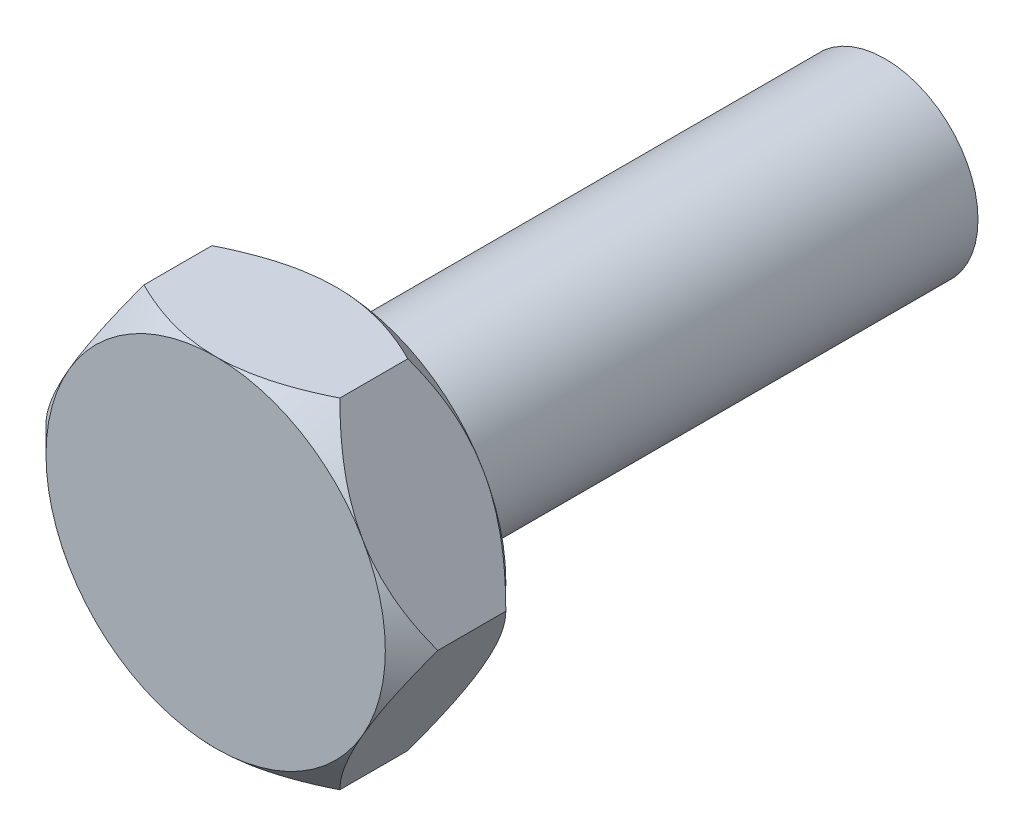
SolidWorks part; units mm, degrees
ref_plane "Front Plane" through (0, 0, 0) normal (0, 0, 1) x (1, 0, 0)
ref_plane "Top Plane" through (0, 0, 0) normal (0, 1, 0) x (1, 0, 0)
ref_plane "Right Plane" through (0, 0, 0) normal (1, 0, 0) x (0, 0, -1)
sketch "Sketch1" plane through (0, 0, 0) normal (0, 0, 1) x (1, 0, 0)
  line L1 (-6.3333, 10.9697) -> (-12.6667, 0)
  line L2 (-12.6667, 0) -> (-6.3333, -10.9697)
  line L3 (-6.3333, -10.9697) -> (6.3333, -10.9697)
  line L4 (6.3333, -10.9697) -> (12.6667, 0)
  line L5 (12.6667, 0) -> (6.3333, 10.9697)
  line L6 (6.3333, 10.9697) -> (-6.3333, 10.9697)
  circle A0 centre (0, 0) radius 10.9697 construction
  dimension "D1" = 19
extrude "Boss-Extrude1" add sketch "Sketch1" along normal mid plane 7.79
sketch "Sketch2" plane through (0, 0, 3.895) normal (0, 0, 1) x (1, 0, 0)
  line L0 (-6.3333, 10.9697) -> (-12.6667, 0) construction
  circle A0 centre (0, 0) radius 10.9697
extrude "Cut-Extrude1" cut sketch "Sketch2" against normal through all draft 45 flip side to cut
mirror "Mirror1" about plane through (0, 0, 0) normal (0, 0, 1) of "Cut-Extrude1"
sketch "Sketch3" plane through (0, 0, -3.895) normal (0, 0, -1) x (-1, 0, 0)
  circle A0 centre (0, 0) radius 6
  dimension "D1" = 12
extrude "Boss-Extrude2" add sketch "Sketch3" along normal blind 35.5
cosmetic thread "Cosmetic Thread1" parameters "D1"=30, "D2"=10.072
